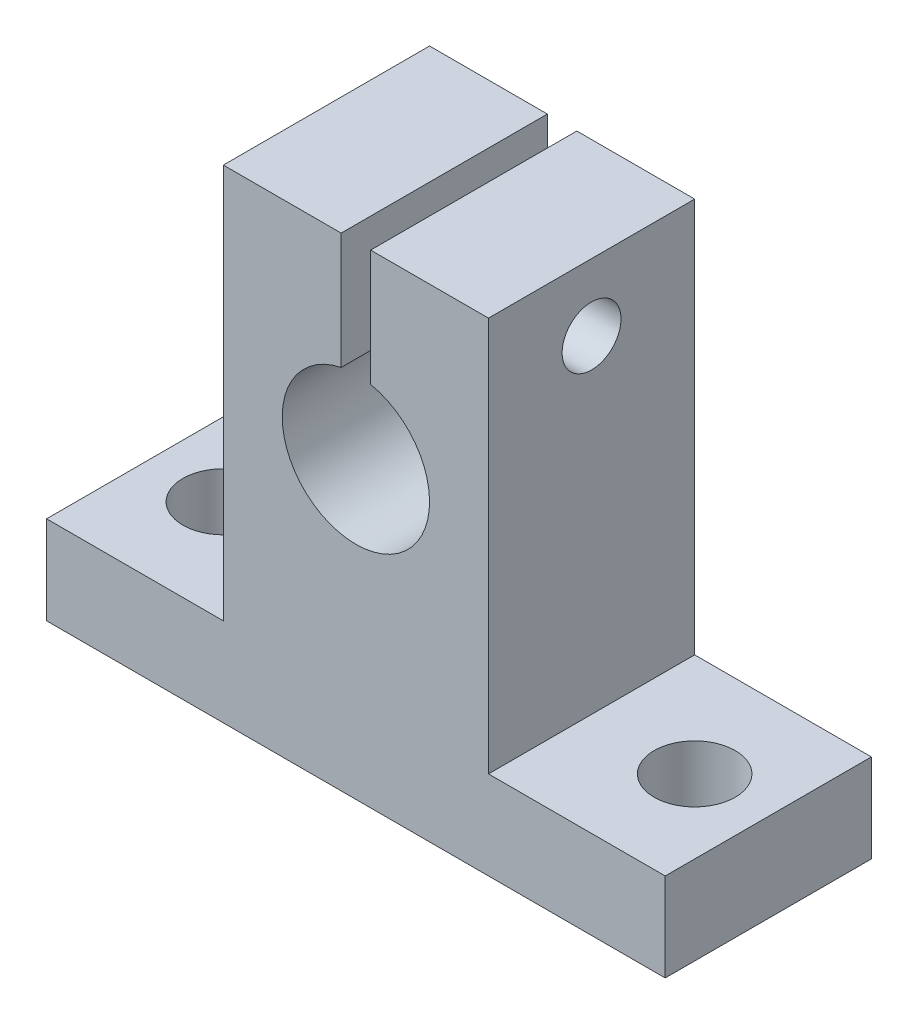
SolidWorks part; units mm, degrees
ref_plane "Plan de face" through (0, 0, 0) normal (0, 0, 1) x (1, 0, 0)
ref_plane "Plan de dessus" through (0, 0, 0) normal (0, 1, 0) x (1, 0, 0)
ref_plane "Plan de droite" through (0, 0, 0) normal (1, 0, 0) x (0, 0, -1)
sketch "Sketch1" plane through (0, 0, 0) normal (0, 0, 1) x (1, 0, 0)
  line L0 (0, 0) -> (42, 0)
  line L1 (42, 0) -> (42, 6)
  line L2 (42, 6) -> (30, 6)
  line L3 (30, 6) -> (30, 32.8)
  line L4 (30, 32.8) -> (22, 32.8)
  line L5 (22, 32.8) -> (22, 24.899)
  line L6 (21, 0) -> (21, 30.8334) construction
  line L7 (20, 32.8) -> (20, 24.899)
  line L8 (12, 32.8) -> (20, 32.8)
  line L9 (12, 6) -> (12, 32.8)
  line L10 (0, 6) -> (12, 6)
  line L11 (0, 0) -> (0, 6)
  arc A0 (20, 24.899) -> (22, 24.899) centre (21, 20) ccw
  dimension "D5" = 5
  dimension "D1" = 42
  dimension "D2" = 6
  dimension "D3" = 20
  dimension "D4" = 18
  dimension "D6" = 32.8
  dimension "D7" = 2
extrude "Boss-Extrude1" add sketch "Sketch1" along normal blind 14
sketch "Sketch2" plane through (0, 6, 0) normal (0, 1, 0) x (1, 0, 0)
  line L2 (0, -7) -> (12, -7) construction
  line L3 (0, -14) -> (0, 0) construction
  line L4 (12, -14) -> (12, 0) construction
  line L5 (21, 0) -> (21, -14) construction
  line L6 (26, 0) -> (16, 0) construction
  line L7 (16, -14) -> (26, -14) construction
  circle A0 centre (5, -7) radius 2.75
  circle A1 centre (37, -7) radius 2.75
  dimension "D1" = 5.5
  dimension "D2" = 5
extrude "Cut-Extrude1" cut sketch "Sketch2" against normal through all
sketch "Sketch3" plane through (12, 0, 0) normal (-1, 0, 0) x (0, 0, 1)
  line L0 (7, 32.8) -> (7, 19.5308) construction
  line L1 (14, 32.8) -> (0, 32.8) construction
  circle A0 centre (7, 28.2542) radius 2
  dimension "D1" = 4
extrude "Cut-Extrude2" cut sketch "Sketch3" against normal through all contours A0
sketch "Sketch4" plane through (12, 0, 0) normal (-1, 0, 0) x (0, 0, 1)
  circle A0 centre (7, 28.2542) radius 3.5
  dimension "D1" = 7
extrude "Cut-Extrude3" cut sketch "Sketch4" against normal blind 3 contours A0
